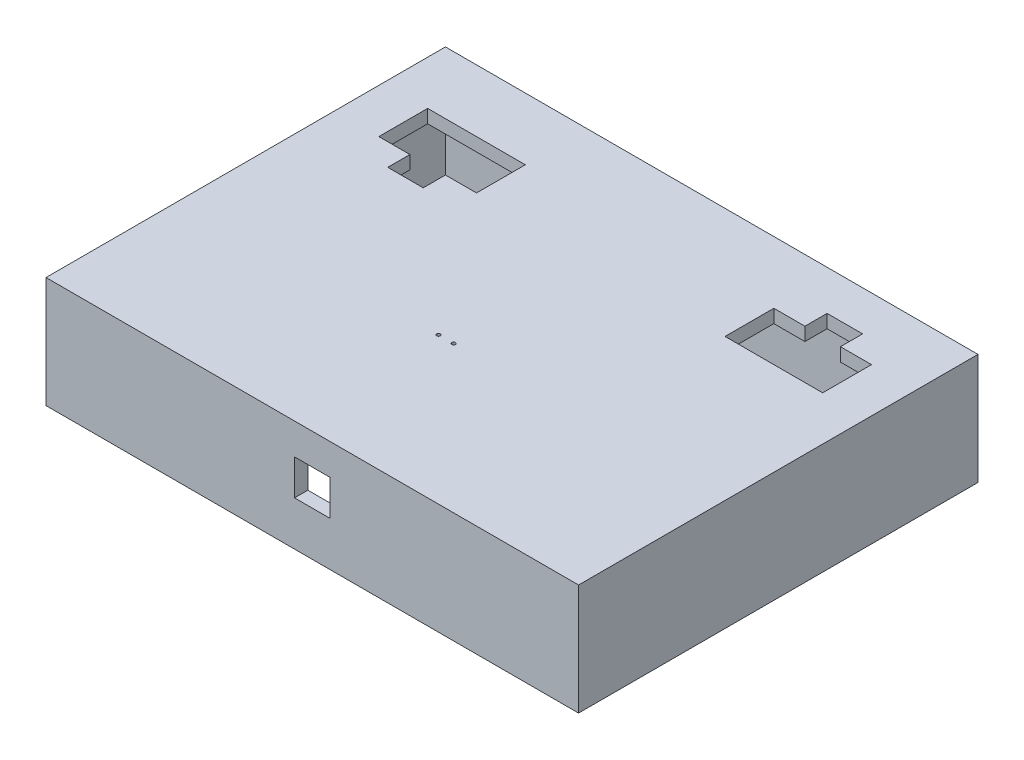
SolidWorks part; units mm, degrees
ref_plane "Front Plane" through (0, 0, 0) normal (0, 0, 1) x (1, 0, 0)
ref_plane "Top Plane" through (0, 0, 0) normal (0, 1, 0) x (1, 0, 0)
ref_plane "Right Plane" through (0, 0, 0) normal (1, 0, 0) x (0, 0, -1)
sketch "Sketch1" plane through (0, 0, 0) normal (0, 1, 0) x (1, 0, 0)
  line L1 (-60, 45) -> (60, 45)
  line L2 (-60, 45) -> (-60, -45)
  line L3 (-60, -45) -> (60, -45)
  line L4 (60, 45) -> (60, -45)
  line L5 (-60, 45) -> (60, -45) construction
  line L6 (-60, -45) -> (60, 45) construction
  point P0 (0, 0)
  dimension "D1" = 120
  dimension "D2" = 90
extrude "Boss-Extrude1" add sketch "Sketch1" along normal blind 25
sketch "Sketch2" plane through (0, 0, 0) normal (0, -1, 0) x (1, 0, 0)
  line L0 (-60, 45) -> (60, 45) construction
  line L1 (-57, 42) -> (57, 42)
  line L2 (-57, 42) -> (-57, -42)
  line L3 (-57, -42) -> (57, -42)
  line L4 (57, 42) -> (57, -42)
  line L5 (-57, 42) -> (57, -42) construction
  line L6 (-57, -42) -> (57, 42) construction
  line L7 (-60, -45) -> (-60, 45) construction
  point P0 (0, 0)
  dimension "D1" = 3
  dimension "D2" = 3
extrude "Cut-Extrude1" cut sketch "Sketch2" against normal blind 22
sketch "Sketch3" plane through (0, 0, 0) normal (0, -1, 0) x (1, 0, 0)
  line L0 (-60, 45) -> (60, 45) construction
  line L1 (-58.5, -43.5) -> (58.5, -43.5)
  line L2 (-58.5, -43.5) -> (-58.5, 43.5)
  line L3 (-58.5, 43.5) -> (58.5, 43.5)
  line L4 (58.5, -43.5) -> (58.5, 43.5)
  line L5 (-58.5, -43.5) -> (58.5, 43.5) construction
  line L6 (-58.5, 43.5) -> (58.5, -43.5) construction
  line L7 (-60, -45) -> (-60, 45) construction
  point P0 (0, 0)
  dimension "D1" = 1.5
  dimension "D2" = 1.5
extrude "Cut-Extrude2" cut sketch "Sketch3" against normal blind 1.5
sketch "Sketch4" plane through (0, 25, 0) normal (0, 1, 0) x (1, 0, 0)
  line L0 (-60, -45) -> (60, -45) construction
  line L1 (28, 31) -> (35, 31)
  line L2 (28, 31) -> (28, 20)
  line L3 (28, 20) -> (50, 20)
  line L4 (50, 31) -> (50, 20)
  line L5 (28, 31) -> (50, 20) construction
  line L6 (28, 20) -> (50, 31) construction
  line L7 (60, -45) -> (60, 45) construction
  line L8 (0, -6.7169) -> (0, 30.1178) construction
  line L9 (-28, 20) -> (-50, 31) construction
  line L10 (35, 36) -> (43, 36)
  line L11 (35, 36) -> (35, 31)
  line L13 (43, 36) -> (43, 31)
  line L14 (35, 36) -> (43, 31) construction
  line L15 (35, 31) -> (43, 36) construction
  line L16 (-28, 31) -> (-50, 20) construction
  line L17 (-50, 31) -> (-50, 20)
  line L18 (-28, 20) -> (-35, 20)
  line L19 (-28, 31) -> (-28, 20)
  line L20 (-28, 31) -> (-50, 31)
  line L22 (43, 31) -> (50, 31)
  line L23 (-43, 20) -> (-50, 20)
  line L25 (-43, 20) -> (-43, 15)
  line L26 (-43, 15) -> (-35, 15)
  line L27 (-35, 20) -> (-35, 15)
  line L28 (-43, 20) -> (-35, 15) construction
  line L29 (-43, 15) -> (-35, 20) construction
  point P0 (39, 25.5)
  point P12 (39, 33.5)
  point P21 (-39, 25.5)
  point P24 (-39, 17.5)
  dimension "D1" = 11
  dimension "D2" = 22
  dimension "D3" = 65
  dimension "D4" = 10
  dimension "D5" = 5
  dimension "D6" = 8
  dimension "D7" = 8
  dimension "D8" = 5
extrude "Cut-Extrude3" cut sketch "Sketch4" against normal blind 11.5
sketch "Sketch5" plane through (0, 0, 45) normal (0, 0, 1) x (1, 0, 0)
  line L0 (-60, 0) -> (60, 0) construction
  line L1 (-4, 18) -> (4, 18)
  line L2 (-4, 18) -> (-4, 10)
  line L3 (-4, 10) -> (4, 10)
  line L4 (4, 18) -> (4, 10)
  line L5 (-4, 18) -> (4, 10) construction
  line L6 (-4, 10) -> (4, 18) construction
  point P0 (0, 14)
  dimension "D1" = 8
  dimension "D2" = 8
  dimension "D3" = 10
extrude "Cut-Extrude4" cut sketch "Sketch5" against normal blind 11.5
sketch "Sketch6" plane through (0, 25, 0) normal (0, 1, 0) x (1, 0, 0)
  circle A0 centre (-4.5924, -11.9593) radius 0.4
  circle A1 centre (-1.1924, -11.9593) radius 0.4
  dimension "D1" = 0.8
  dimension "D2" = 0.8
  dimension "D3" = 3.4
extrude "Cut-Extrude6" cut sketch "Sketch6" against normal blind 21.5
